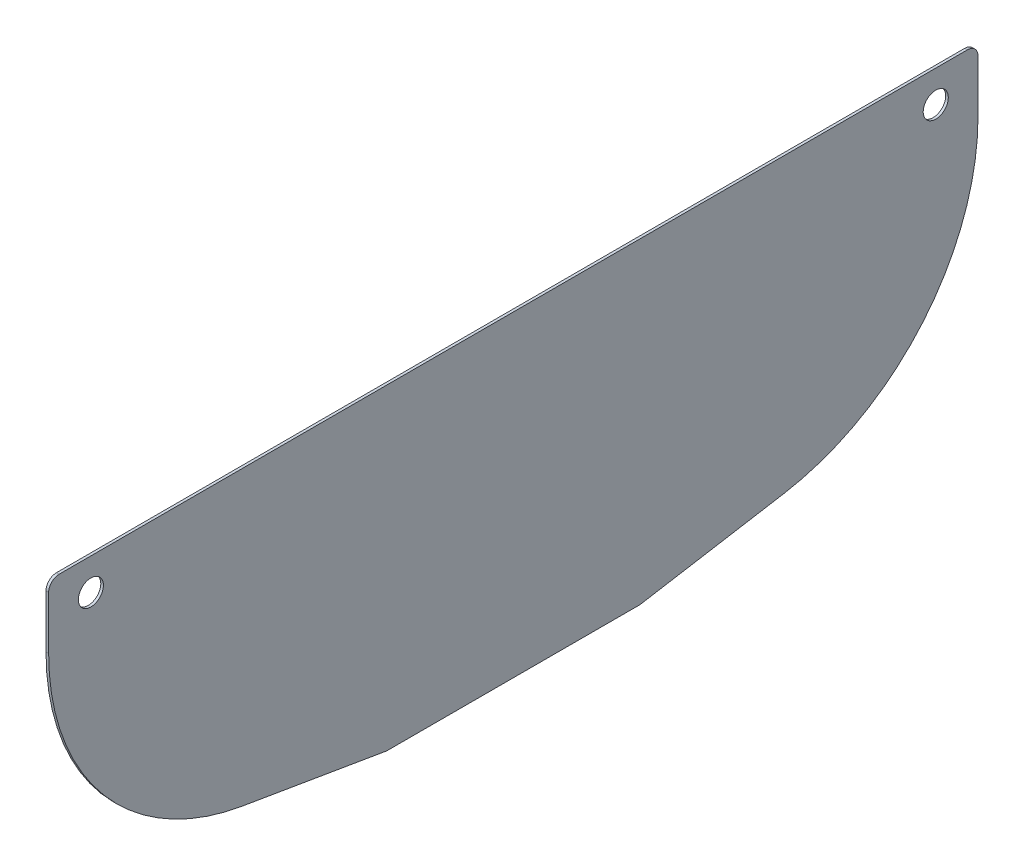
SolidWorks part; units mm, degrees
material "PC High Viscosity"
ref_plane "Front Plane" through (0, 0, 0) normal (0, 0, 1) x (1, 0, 0)
ref_plane "Top Plane" through (0, 0, 0) normal (0, 1, 0) x (1, 0, 0)
ref_plane "Right Plane" through (0, 0, 0) normal (1, 0, 0) x (0, 0, -1)
sketch "Sketch1" plane through (0, 0, 0) normal (1, 0, 0) x (0, 0, -1)
  line L2 (-558.8, 609.6) -> (-558.8, 685.8)
  line L3 (-558.8, 685.8) -> (558.8, 685.8)
  line L4 (558.8, 685.8) -> (558.8, 609.6)
  line L6 (152.4, 304.8) -> (325.92, 334.1)
  line L8 (0, 0) -> (0, 941.2231) construction
  line L9 (152.4, 304.8) -> (-152.4, 304.8)
  line L10 (-152.4, 304.8) -> (-325.92, 334.1)
  circle A0 centre (-508, 647.7) radius 15.0813
  circle A1 centre (508, 647.7) radius 15.0813
  arc A2 (325.92, 334.1) -> (558.8, 609.6) centre (279.4, 609.6) ccw
  arc A3 (-325.92, 334.1) -> (-558.8, 609.6) centre (-279.4, 609.6) cw
  dimension "D1" = 30.1625
  dimension "D11" = 609.6
  dimension "D5" = 152.4
  dimension "D2" = 1016
  dimension "D3" = 508
  dimension "D4" = 647.7
  dimension "D6" = 558.8
  dimension "D7" = 685.8
  dimension "D8" = 38.1
  dimension "D9" = 304.8
  dimension "D10" = 279.4
  dimension "D13" = 50.8
  dimension "D14" = 152.4
extrude "Boss-Extrude1" add sketch "Sketch1" along normal blind 3.175
fillet "Fillet1" radius 12.7 4 edges at (1.5875, 685.8, -558.8) (1.5875, 685.8, 558.8) (1.5875, 304.8, 152.4) (1.5875, 304.8, -152.4)
sketch "Sketch4" plane through (3.175, 0, 0) normal (1, 0, 0) x (0, 0, -1)
  arc A0 (-500.9147, 634.3868) -> (500.9147, 634.3868) centre (0, 909.5172) ccw construction
  circle A1 centre (-508, 647.7) radius 15.0812 construction
  circle A2 centre (508, 647.7) radius 15.0813 construction
  circle A3 centre (-508, 647.7) radius 15.0813 construction
  circle A4 centre (508, 647.7) radius 15.0813 construction
  circle A5 centre (0, 345.9547) radius 3.3655
  circle A6 centre (0, 330.0797) radius 3.3655
  point P12 (0, 338.0172)
  dimension "D1" = 571.5
  dimension "D2" = 6.731
  dimension "D3" = 15.875
  dimension "D4" = 7.9375
